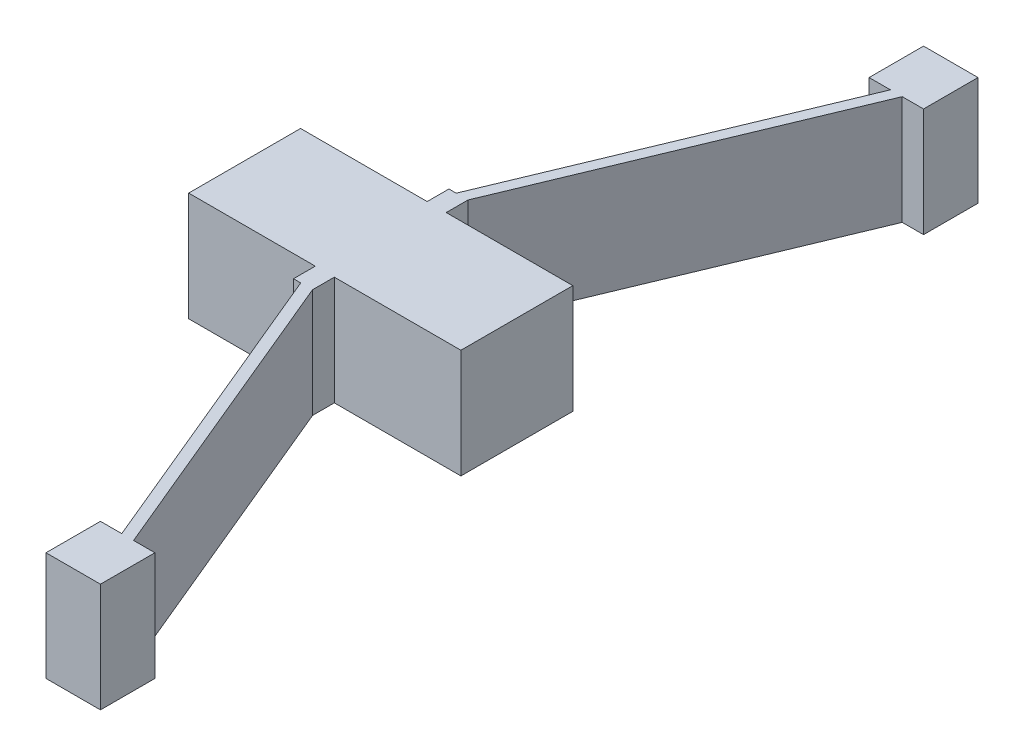
SolidWorks part; units mm, degrees
ref_plane "Front Plane" through (0, 0, 0) normal (0, 0, 1) x (1, 0, 0)
ref_plane "Top Plane" through (0, 0, 0) normal (0, 1, 0) x (1, 0, 0)
ref_plane "Right Plane" through (0, 0, 0) normal (1, 0, 0) x (0, 0, -1)
sketch "Sketch1" plane through (0, 0, 0) normal (0, 1, 0) x (1, 0, 0)
  line L0 (0, 0) -> (0.1, 0) construction
  line L1 (0, 0.0206) -> (0.1, 0.0206)
  line L2 (0, 0.0206) -> (0, -0.0206)
  line L3 (0, -0.0206) -> (0.1, -0.0206)
  line L4 (0.1, 0.0206) -> (0.1, -0.0206)
  line L5 (0.0982, 0.1612) -> (0.0982, 0.1412) construction
  line L6 (0.0535, 0.0206) -> (0.0465, 0.0206)
  line L7 (0.0535, 0.0206) -> (0.0535, 0.0286)
  line L8 (0.0535, 0.0286) -> (0.0465, 0.0286)
  line L9 (0.0465, 0.0206) -> (0.0465, 0.0286)
  line L10 (0.0882, 0.1612) -> (0.1082, 0.1612)
  line L11 (0.0882, 0.1612) -> (0.0882, 0.1412)
  line L12 (0.0882, 0.1412) -> (0.1082, 0.1412)
  line L13 (0.1082, 0.1612) -> (0.1082, 0.1412)
  line L14 (0.0535, 0.0286) -> (0.1004, 0.1412)
  line L15 (0.1004, 0.1412) -> (0.0961, 0.1412)
  line L16 (0.0961, 0.1412) -> (0.0492, 0.0286)
  line L17 (0.0492, 0.0286) -> (0.0535, 0.0286)
  line L18 (0.0535, 0.0286) -> (0.0703, 0.0286) construction
  line L19 (0.0882, -0.1412) -> (0.1082, -0.1412)
  line L20 (0.1082, -0.1612) -> (0.1082, -0.1412)
  line L21 (0.0882, -0.1612) -> (0.1082, -0.1612)
  line L22 (0.0882, -0.1612) -> (0.0882, -0.1412)
  line L23 (0.0492, -0.0286) -> (0.0535, -0.0286)
  line L24 (0.0961, -0.1412) -> (0.0492, -0.0286)
  line L25 (0.1004, -0.1412) -> (0.0961, -0.1412)
  line L26 (0.0535, -0.0286) -> (0.1004, -0.1412)
  line L27 (0.0535, -0.0286) -> (0.0465, -0.0286)
  line L28 (0.0465, -0.0206) -> (0.0465, -0.0286)
  line L29 (0.0535, -0.0206) -> (0.0465, -0.0206)
  line L30 (0.0535, -0.0206) -> (0.0535, -0.0286)
  point P6 (0.05, 0.0206)
  point P12 (0.05, 0.0286)
  dimension "D1" = 0.0411
  dimension "D2" = 0.1
  dimension "D3" = 0.008
  dimension "D4" = 0.007
  dimension "D5" = 0.02
  dimension "D6" = 0.02
  dimension "D7" = 0.004
  dimension "D8" = 0.122
  dimension "D9" = 67.4
extrude "Boss-Extrude1" add sketch "Sketch1" along normal blind 0.04 contours L4 L1 L2 L3 | L9 L1 L7 L8 | L12 L16 L8 L14 | L27 L28 L29 L30 | L26 L25 L24 L23 | L19 L20 L21 L22
